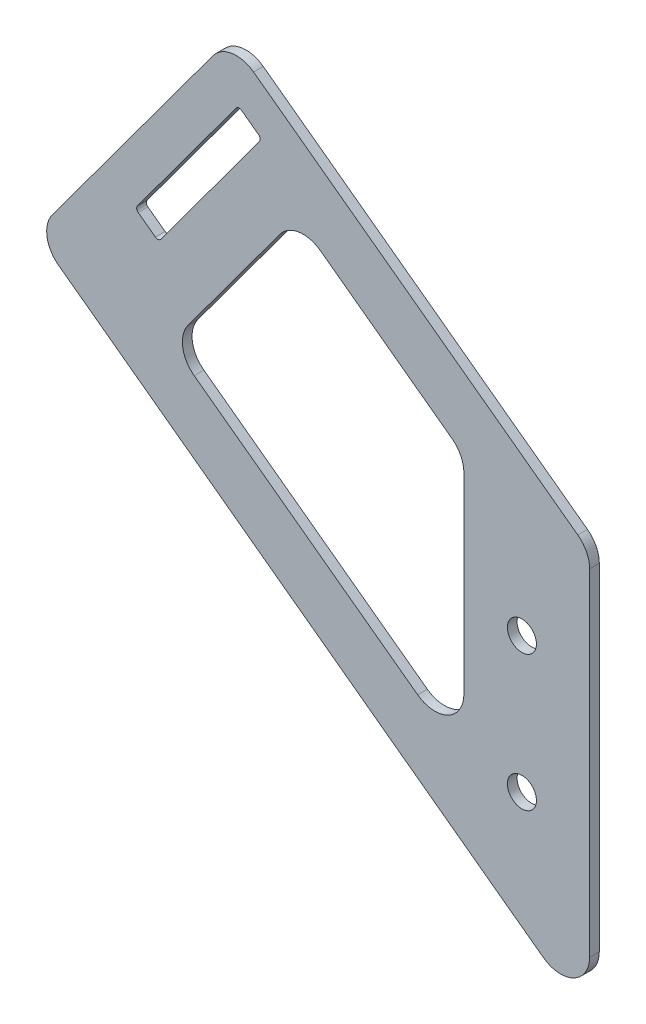
SolidWorks part; units mm, degrees
ref_plane "Front Plane" through (0, 0, 0) normal (0, 0, 1) x (1, 0, 0)
ref_plane "Top Plane" through (0, 0, 0) normal (0, 1, 0) x (1, 0, 0)
ref_plane "Right Plane" through (0, 0, 0) normal (1, 0, 0) x (0, 0, -1)
sketch "Sketch1" plane through (0, 0, 0) normal (0, 0, 1) x (1, 0, 0)
  line L1 (-154.8235, 399.6982) -> (-162.4926, 405.3473) construction
  line L4 (-155.8461, 400.4514) -> (-161.47, 404.594)
  line L5 (-129.3515, 450.3389) -> (-161.7394, 406.3698)
  line L6 (-121.9518, 446.4656) -> (-127.5758, 450.6082)
  line L7 (-35.56, 302.8376) -> (-35.56, 347.2876) construction
  line L9 (-154.0703, 400.7207) -> (-121.6825, 444.6898)
  line L13 (-154.8235, 399.6982) -> (-120.9293, 445.7124) construction
  line L15 (-13.335, 248.1566) -> (-13.335, 382.2315)
  line L16 (-10.16, 466.8115) -> (-10.16, 383.0274) construction
  line L17 (-13.335, 382.2315) -> (-131.2917, 469.1188)
  line L18 (-131.2917, 469.1188) -> (-195.3141, 382.2032)
  line L19 (-195.3141, 382.2032) -> (-13.335, 248.1566)
  line L20 (-109.3573, 429.3016) -> (-150.7836, 373.0621)
  line L21 (-109.3573, 429.3016) -> (-54.61, 388.9745)
  line L22 (-150.7836, 373.0621) -> (-96.0363, 332.735)
  line L23 (-54.61, 388.9745) -> (-96.0363, 332.735)
  line L24 (-54.61, 388.9745) -> (-54.61, 302.2202)
  line L25 (-54.61, 302.2202) -> (-96.0363, 332.735)
  circle A1 centre (-35.56, 347.2876) radius 4.7625 construction
  circle A2 centre (-35.56, 347.2876) radius 4.7625
  circle A3 centre (-35.56, 302.8376) radius 4.7625
  arc A8 (-129.3515, 450.3389) -> (-127.5758, 450.6082) centre (-128.329, 449.5857) cw
  arc A9 (-121.9518, 446.4656) -> (-121.6825, 444.6898) centre (-122.705, 445.443) cw
  arc A10 (-155.8461, 400.4514) -> (-154.0703, 400.7207) centre (-155.0929, 401.474) ccw
  arc A11 (-161.47, 404.594) -> (-161.7394, 406.3698) centre (-160.7168, 405.6166) cw
  circle A12 centre (-35.56, 302.8376) radius 4.7625 construction
  point P20 (-135.9433, 484.2177)
  dimension "D1" = 3.175
  dimension "D5" = 19.05
  dimension "D6" = 1.27
  dimension "D2" = 12.7
  dimension "D3" = 38.1
  dimension "D4" = 12.7
  dimension "D7" = 9.525
  dimension "D8" = 57.15
  dimension "D9" = 19.05
  dimension "D10" = 19.05
  dimension "D11" = 19.05
extrude "Boss-Extrude1" add sketch "Sketch1" along normal blind 3.175
fillet "Fillet1" radius 9.525 8 edges at (-13.335, 248.1566, 1.5875) (-13.335, 382.2315, 1.5875) (-131.2917, 469.1188, 1.5875) (-195.3141, 382.2032, 1.5875) (-150.7836, 373.0621, 1.5875) (-54.61, 302.2202, 1.5875) (-54.61, 388.9745, 1.5875) (-109.3573, 429.3016, 1.5875)
